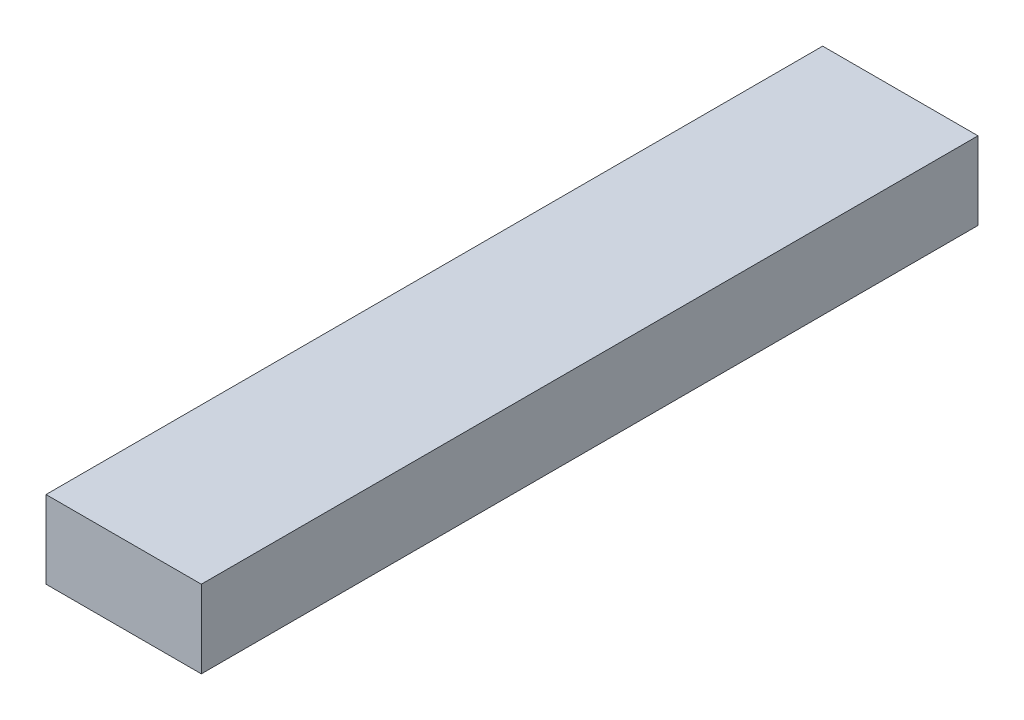
SolidWorks part; units mm, degrees
ref_plane "Front" through (0, 0, 0) normal (0, 0, 1) x (1, 0, 0)
ref_plane "Top" through (0, 0, 0) normal (0, 1, 0) x (1, 0, 0)
ref_plane "Right" through (0, 0, 0) normal (1, 0, 0) x (0, 0, -1)
sketch "Эскиз1" plane through (0, 0, 0) normal (0, 0, 1) x (1, 0, 0)
  line L1 (-23.9098, 22.6316) -> (56.0902, 22.6316)
  line L2 (-23.9098, 22.6316) -> (-23.9098, -17.3684)
  line L3 (-23.9098, -17.3684) -> (56.0902, -17.3684)
  line L4 (56.0902, 22.6316) -> (56.0902, -17.3684)
  dimension "D1" = 40
  dimension "D2" = 80
extrude "Бобышка-Вытянуть1" add sketch "Эскиз1" along normal blind 400
